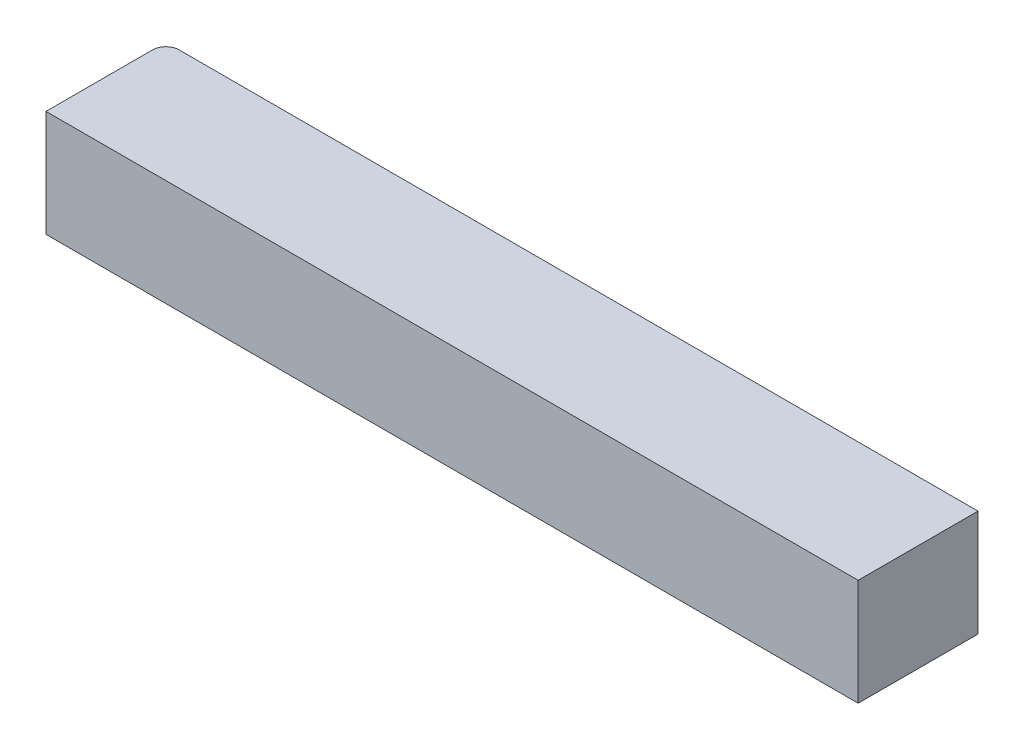
SolidWorks part; units mm, degrees
material "Air"
ref_plane "Front Plane" through (0, 0, 0) normal (0, 0, 1) x (1, 0, 0)
ref_plane "Top Plane" through (0, 0, 0) normal (0, 1, 0) x (1, 0, 0)
ref_plane "Right Plane" through (0, 0, 0) normal (1, 0, 0) x (0, 0, -1)
sketch "Sketch1" plane through (0, 0, 0) normal (0, 1, 0) x (1, 0, 0)
  line L0 (-30.5, 4.5) -> (30.5, -4.5) construction
  line L1 (-29.5, 4.5) -> (30.5, 4.5)
  line L2 (-30.5, 3.5) -> (-30.5, -4.5)
  line L3 (-30.5, -4.5) -> (30.5, -4.5)
  line L4 (30.5, 4.5) -> (30.5, -4.5)
  line L5 (-30.5, 4.5) -> (-30.5, 3.5) construction
  line L6 (-30.5, 4.5) -> (-29.5, 4.5) construction
  arc A0 (-30.5, 3.5) -> (-29.5, 4.5) centre (-29.5, 3.5) cw
  point P4 (-29.5, 4.5)
  point P5 (-30.5, 3.5)
  dimension "D1" = 61
  dimension "D2" = 9
  dimension "D3" = 1
  dimension "D4" = 1
extrude "Boss-Extrude1" add sketch "Sketch1" along normal blind 8
